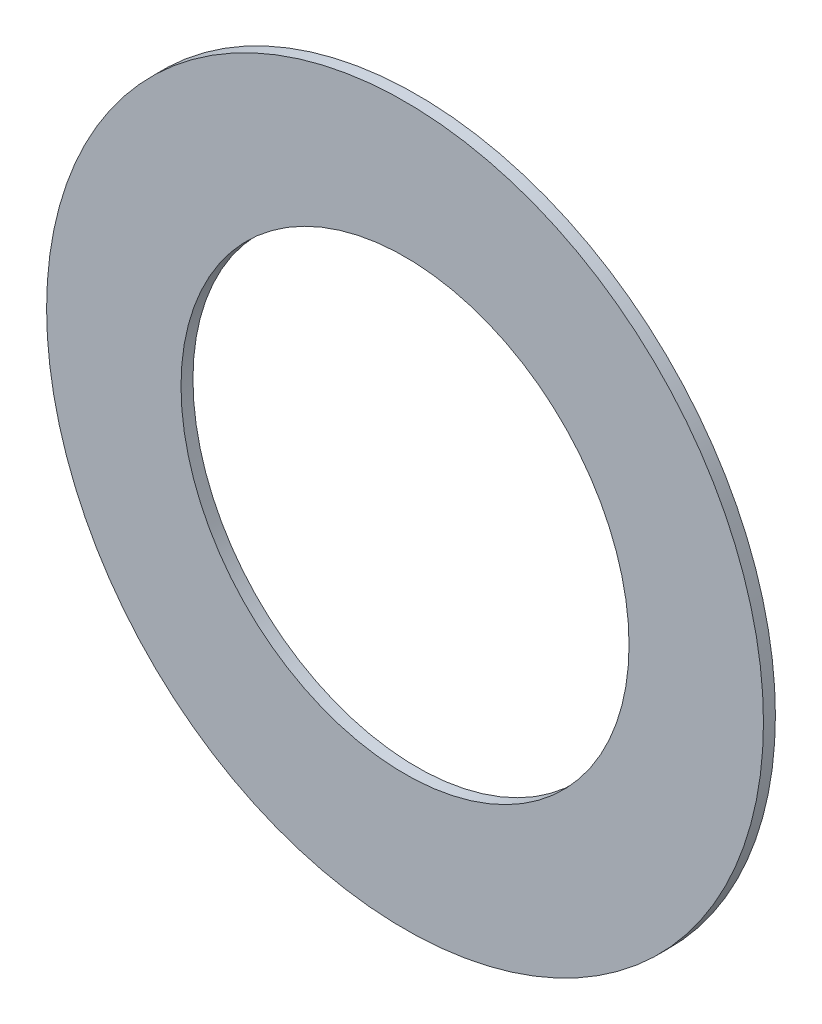
SolidWorks part; units mm, degrees
ref_plane "Front Plane" through (0, 0, 0) normal (0, 0, 1) x (1, 0, 0)
ref_plane "Top Plane" through (0, 0, 0) normal (0, 1, 0) x (1, 0, 0)
ref_plane "Right Plane" through (0, 0, 0) normal (1, 0, 0) x (0, 0, -1)
sketch "Sketch1" plane through (0, 0, 0) normal (0, 0, 1) x (1, 0, 0)
  circle A0 centre (0, 0) radius 15.24
  dimension "D1" = 30.48
extrude "Boss-Extrude1" add sketch "Sketch1" along normal blind 0.508
sketch "Sketch2" plane through (0, 0, 0.508) normal (0, 0, 1) x (1, 0, 0)
  circle A0 centre (0, 0) radius 9.525
  dimension "D1" = 19.05
extrude "Cut-Extrude1" cut sketch "Sketch2" against normal through all
